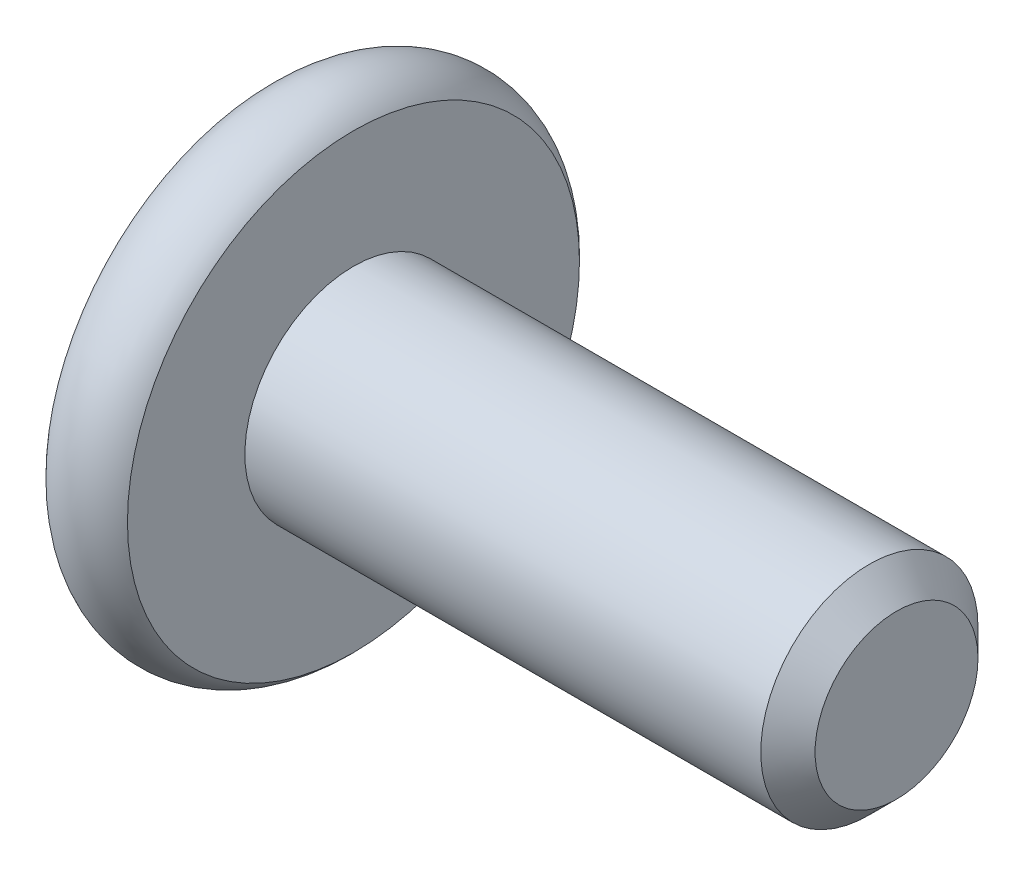
SolidWorks part; units mm, degrees
material "Plain Carbon Steel"
ref_plane "Front Plane" through (0, 0, 0) normal (0, 0, 1) x (1, 0, 0)
ref_plane "Top Plane" through (0, 0, 0) normal (0, 1, 0) x (1, 0, 0)
ref_plane "Right Plane" through (0, 0, 0) normal (1, 0, 0) x (0, 0, -1)
other "M5 x 15"
sketch "Sketch2" plane through (0, 0, 0) normal (1, 0, 0) x (0, 0, -1)
  circle A0 centre (0, 0) radius 2
  dimension "D1" = 4
extrude "Boss-Extrude1" add sketch "Sketch2" against normal blind 10
chamfer "Chamfer1" distance 0.5 angle 45 1 edges at (0, 0, -2)
sketch "Sketch6" plane through (0, 0, 0) normal (0, 0, 1) x (1, 0, 0)
  line L0 (-11.5, 0) -> (-11.5, 4.1614)
  line L1 (-11.5, 0) -> (-10, 0)
  line L2 (-10.75, 0) -> (-10.75, 3.5) construction
  line L6 (-10, 4.1614) -> (-10, 0)
  line L8 (-10, 0) -> (-14.6471, 0) construction
  line L10 (-10, 2) -> (-10, -2) construction
  arc A0 (-11.5, 4.1614) -> (-10, 4.1614) centre (-10.75, 3.5) cw
  dimension "D3" = 1
  dimension "D1" = 1.5
  dimension "D2" = 9
revolve "Revolve1" add sketch "Sketch6" angle 360 about L8
sketch "Sketch7" plane through (-11.5, 0, 0) normal (-1, 0, 0) x (0, 0, 1)
  line L1 (0, 1.7321) -> (-1.5, 0.866)
  line L2 (-1.5, 0.866) -> (-1.5, -0.866)
  line L3 (-1.5, -0.866) -> (0, -1.7321)
  line L4 (0, -1.7321) -> (1.5, -0.866)
  line L5 (1.5, -0.866) -> (1.5, 0.866)
  line L6 (1.5, 0.866) -> (0, 1.7321)
  circle A0 centre (0, 0) radius 1.5 construction
  dimension "D1" = 3
extrude "Cut-Extrude1" cut sketch "Sketch7" against normal blind 2.3
sketch "Sketch8" plane through (-11.5, 0, 0) normal (-1, 0, 0) x (0, 0, 1)
  circle A0 centre (0, 0) radius 1.7821
  dimension "D1" = 0.05
extrude "Cut-Extrude2" cut sketch "Sketch8" against normal blind 1 draft 45
